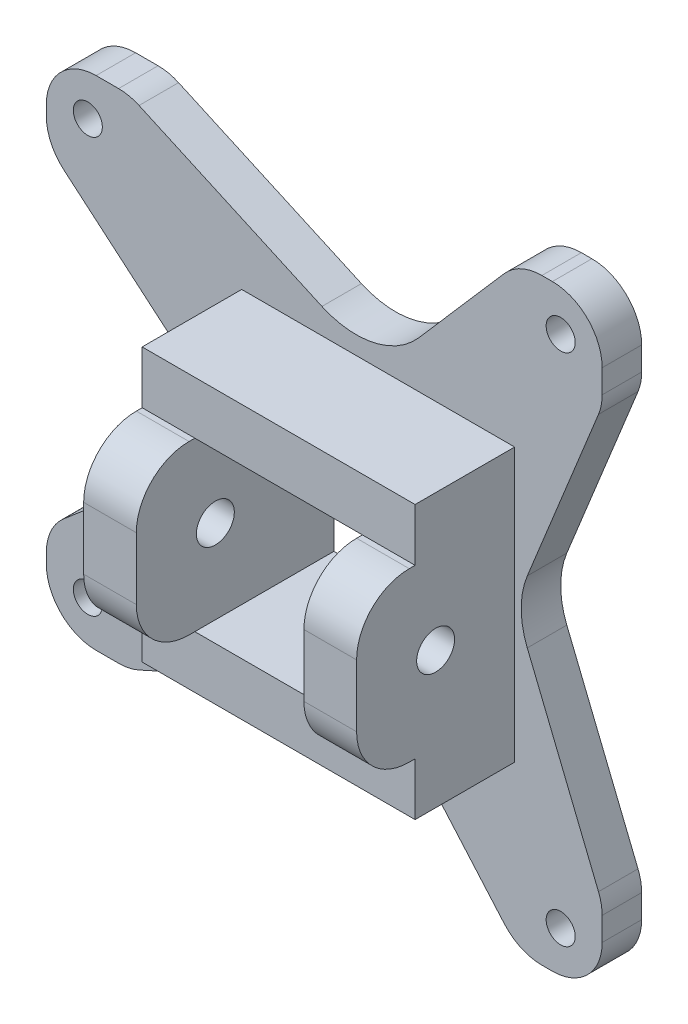
SolidWorks part; units mm, degrees
ref_plane "Front Plane" through (0, 0, 0) normal (0, 0, 1) x (1, 0, 0)
ref_plane "Top Plane" through (0, 0, 0) normal (0, 1, 0) x (1, 0, 0)
ref_plane "Right Plane" through (0, 0, 0) normal (1, 0, 0) x (0, 0, -1)
sketch "Sketch1" plane through (0, 0, 0) normal (0, 0, 1) x (1, 0, 0)
  line L0 (-30, -30) -> (0, -16.45)
  line L1 (-10.1, -10.1) -> (10.1, -10.1)
  line L2 (-10.1, -10.1) -> (-10.1, 10.1)
  line L3 (-10.1, 10.1) -> (10.1, 10.1)
  line L4 (10.1, -10.1) -> (10.1, 10.1)
  line L5 (-10.1, -10.1) -> (10.1, 10.1) construction
  line L6 (-10.1, 10.1) -> (10.1, -10.1) construction
  line L7 (-40, 20) -> (-30, 20) construction
  line L8 (-40, 20) -> (-40, 30)
  line L9 (-40, 30) -> (-30, 30)
  line L10 (-30, 20) -> (-30, 30) construction
  line L11 (-40, 20) -> (-30, 30) construction
  line L12 (-40, 30) -> (-30, 20) construction
  line L13 (17, 26) -> (27, 26) construction
  line L14 (17, 26) -> (17, 36) construction
  line L15 (17, 36) -> (27, 36)
  line L16 (27, 26) -> (27, 36)
  line L17 (17, 26) -> (27, 36) construction
  line L18 (17, 36) -> (27, 26) construction
  line L19 (17, -36) -> (27, -36)
  line L20 (17, -36) -> (17, -26) construction
  line L21 (17, -26) -> (27, -26) construction
  line L22 (27, -36) -> (27, -26)
  line L23 (17, -36) -> (27, -26) construction
  line L24 (17, -26) -> (27, -36) construction
  line L25 (-40, -30) -> (-30, -30)
  line L26 (-40, -30) -> (-40, -20)
  line L27 (-40, -20) -> (-30, -20) construction
  line L28 (-30, -30) -> (-30, -20) construction
  line L29 (-40, -30) -> (-30, -20) construction
  line L30 (-40, -20) -> (-30, -30) construction
  line L31 (-16.45, -16.45) -> (16.45, -16.45) construction
  line L32 (-16.45, -16.45) -> (-16.45, 16.45) construction
  line L33 (-16.45, 16.45) -> (16.45, 16.45) construction
  line L34 (16.45, -16.45) -> (16.45, 16.45) construction
  line L35 (-16.45, -16.45) -> (16.45, 16.45) construction
  line L36 (-16.45, 16.45) -> (16.45, -16.45) construction
  line L37 (0, -16.45) -> (17, -36)
  line L38 (27, -26) -> (16.45, 0)
  line L39 (16.45, 0) -> (27, 26)
  line L40 (17, 36) -> (0, 16.45)
  line L41 (0, 16.45) -> (-30, 30)
  line L42 (-40, 20) -> (-16.45, 0)
  line L43 (-16.45, 0) -> (-40, -20)
  circle A0 centre (22, 31) radius 1.75
  circle A1 centre (22, -31) radius 1.75
  circle A2 centre (-35, 25) radius 1.75
  circle A3 centre (-35, -25) radius 1.75
  point P15 (0, 0)
  point P30 (0, 0)
  dimension "D7" = 3.5
  dimension "D1" = 22
  dimension "D2" = 35
  dimension "D3" = 31
  dimension "D4" = 31
  dimension "D5" = 25
  dimension "D6" = 25
  dimension "D8" = 20.2
  dimension "D9" = 10
  dimension "D10" = 6.35
extrude "Boss-Extrude1" add sketch "Sketch1" along normal blind 4.7625
fillet "Fillet1" radius 6 12 edges at (-40, 20, 2.3813) (-40, 30, 2.3813) (-30, 30, 2.3813) (17, 36, 2.3813) (27, 36, 2.3813) (27, 26, 2.3813) (27, -26, 2.3813) (27, -36, 2.3813) (-40, -20, 2.3813) (-40, -30, 2.3813) (-30, -30, 2.3813) (17, -36, 2.3813)
fillet "Fillet2" radius 10 4 edges at (0, -16.45, 2.3813) (-16.45, 0, 2.3813) (0, 16.45, 2.3813) (16.45, 0, 2.3813)
sketch "Sketch2" plane through (0, 0, 4.7625) normal (0, 0, 1) x (1, 0, 0)
  line L1 (10.1, 10.1) -> (16.45, 10.1)
  line L2 (10.1, 10.1) -> (10.1, -10.1)
  line L3 (10.1, -10.1) -> (16.45, -10.1)
  line L4 (16.45, 10.1) -> (16.45, -10.1)
  line L5 (-10.1, 10.1) -> (-16.45, 10.1)
  line L6 (-10.1, 10.1) -> (-10.1, -10.1)
  line L7 (-10.1, -10.1) -> (-16.45, -10.1)
  line L8 (-16.45, 10.1) -> (-16.45, -10.1)
  dimension "D1" = 6.35
extrude "Boss-Extrude2" add sketch "Sketch2" along normal blind 19.05
sketch "Sketch3" plane through (16.45, 0, 0) normal (1, 0, 0) x (0, 0, -1)
  line L0 (-4.7625, 0) -> (-23.8125, 0) construction
  line L1 (-4.7625, -10.1) -> (-4.7625, 10.1) construction
  line L2 (-23.8125, -10.1) -> (-23.8125, 10.1) construction
  circle A0 centre (-14.2875, 0) radius 2.286
  dimension "D1" = 4.572
extrude "Cut-Extrude1" cut sketch "Sketch3" against normal through all
sketch "Sketch4" plane through (0, 0, 4.7625) normal (0, 0, 1) x (1, 0, 0)
  line L1 (16.45, 10.1) -> (-16.45, 10.1)
  line L2 (16.45, 10.1) -> (16.45, 16.45)
  line L3 (16.45, 16.45) -> (-16.45, 16.45)
  line L4 (-16.45, 10.1) -> (-16.45, 16.45)
  line L5 (16.45, -10.1) -> (-16.45, -10.1)
  line L6 (16.45, -10.1) -> (16.45, -16.45)
  line L7 (16.45, -16.45) -> (-16.45, -16.45)
  line L8 (-16.45, -10.1) -> (-16.45, -16.45)
  dimension "D1" = 6.35
extrude "Boss-Extrude3" add sketch "Sketch4" along normal blind 12
fillet "Fillet5" radius 6.35 4 edges at (13.275, -10.1, 23.8125) (13.275, 10.1, 23.8125) (-13.275, 10.1, 23.8125) (-13.275, -10.1, 23.8125)
